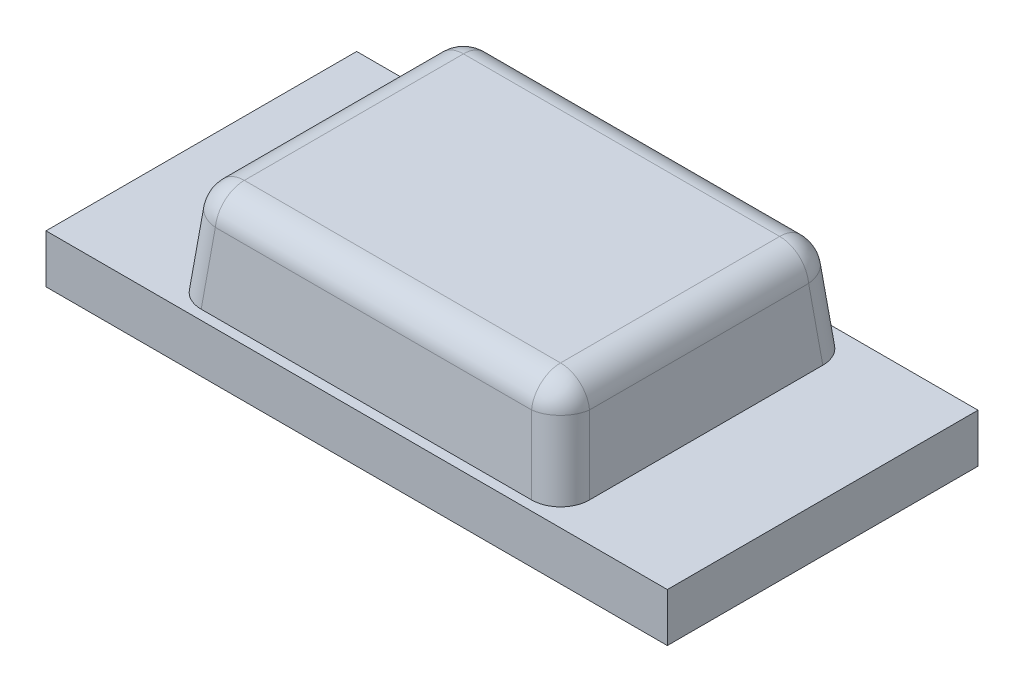
SolidWorks part; units mm, degrees
ref_plane "Front Plane" through (0, 0, 0) normal (0, 0, 1) x (1, 0, 0)
ref_plane "Top Plane" through (0, 0, 0) normal (0, 1, 0) x (1, 0, 0)
ref_plane "Right Plane" through (0, 0, 0) normal (1, 0, 0) x (0, 0, -1)
sketch "Sketch2" plane through (0, 0, 0) normal (0, 1, 0) x (1, 0, 0)
  line L1 (-1.6, -0.8) -> (1.6, -0.8)
  line L2 (-1.6, -0.8) -> (-1.6, 0.8)
  line L3 (-1.6, 0.8) -> (1.6, 0.8)
  line L4 (1.6, -0.8) -> (1.6, 0.8)
  line L5 (-1.6, -0.8) -> (1.6, 0.8) construction
  line L6 (-1.6, 0.8) -> (1.6, -0.8) construction
  point P0 (0, 0)
  dimension "D1" = 1.6
  dimension "D2" = 3.2
extrude "Boss-Extrude1" add sketch "Sketch2" along normal blind 0.25
sketch "Sketch4" plane through (0, 0.25, 0) normal (0, 1, 0) x (1, 0, 0)
  line L0 (1.6, 0.8) -> (-1.6, 0.8) construction
  line L1 (-1, -0.75) -> (1, -0.75)
  line L2 (-1, -0.75) -> (-1, 0.75)
  line L3 (-1, 0.75) -> (1, 0.75)
  line L4 (1, -0.75) -> (1, 0.75)
  line L5 (-1, -0.75) -> (1, 0.75) construction
  line L6 (-1, 0.75) -> (1, -0.75) construction
  point P0 (0, 0)
  dimension "D1" = 2
  dimension "D2" = 0.05
extrude "Boss-Extrude2" add sketch "Sketch4" along normal blind 0.5 draft 5.71
fillet "Fillet1" radius 0.15 8 edges at (0, 0.75, 0.7) (-0.95, 0.75, 0) (0, 0.75, -0.7) (0.95, 0.75, 0) (-0.975, 0.5, -0.725) (0.975, 0.5, -0.725) (0.975, 0.5, 0.725) (-0.975, 0.5, 0.725)
